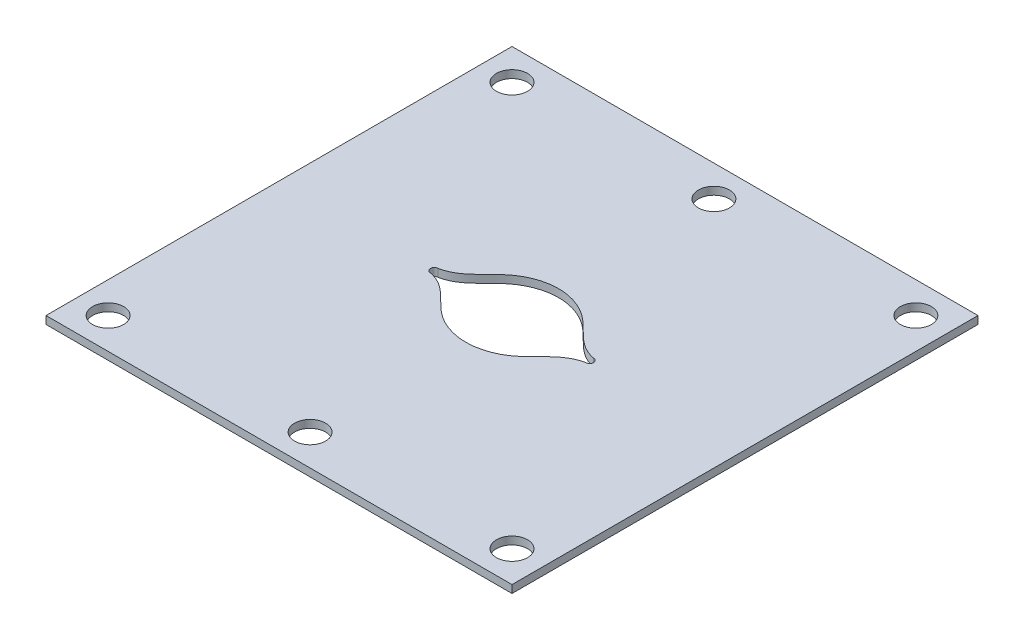
SolidWorks part; units mm, degrees
ref_plane "Front Plane" through (0, 0, 0) normal (0, 0, 1) x (1, 0, 0)
ref_plane "Top Plane" through (0, 0, 0) normal (0, 1, 0) x (1, 0, 0)
ref_plane "Right Plane" through (0, 0, 0) normal (1, 0, 0) x (0, 0, -1)
sketch "Sketch1" plane through (0, 0, 0) normal (0, 1, 0) x (1, 0, 0)
  line L1 (30, -30) -> (-30, -30)
  line L2 (30, -30) -> (30, 30)
  line L3 (30, 30) -> (-30, 30)
  line L4 (-30, -30) -> (-30, 30)
  line L5 (30, -30) -> (-30, 30) construction
  line L6 (30, 30) -> (-30, -30) construction
  point P0 (0, 0)
  dimension "D1" = 60
  dimension "D2" = 60
extrude "Boss-Extrude1" add sketch "Sketch1" along normal blind 1
sketch "Sketch2" plane through (0, 1, 0) normal (0, 1, 0) x (1, 0, 0)
  line L0 (30, 30) -> (-30, 30) construction
  line L2 (-30, 30) -> (-30, -30) construction
  line L3 (30, -30) -> (30, 30) construction
  line L5 (-30, -30) -> (30, -30) construction
  line L7 (-30, 30) -> (-30, -30) construction
  circle A0 centre (-26, 26) radius 2
  circle A1 centre (0, 26) radius 2
  circle A2 centre (26, 26) radius 2
  circle A3 centre (26, -26) radius 2
  circle A4 centre (0, -26) radius 2
  circle A5 centre (-26, -26) radius 2
  dimension "D1" = 4
  dimension "D5" = 4
  dimension "D7" = 4
  dimension "D10" = 4
  dimension "D16" = 4
  dimension "D17" = 4
  dimension "D2" = 4
  dimension "D3" = 4
  dimension "D4" = 4
  dimension "D6" = 0
  dimension "D8" = 4
  dimension "D9" = 4
  dimension "D11" = 4
  dimension "D12" = 4
  dimension "D13" = 4
  dimension "D14" = 4
  dimension "D15" = 4
  dimension "D18" = 0
extrude "Cut-Extrude1" cut sketch "Sketch2" against normal through all
sketch "Sketch3" plane through (0, 1, 0) normal (0, 1, 0) x (1, 0, 0)
  circle A0 centre (10, 0) radius 0.5
  circle A1 centre (-10, 0) radius 0.5
  dimension "D3" = 1
  dimension "D4" = 1
  dimension "D1" = 20
  dimension "D2" = 10
extrude "Cut-Extrude2" cut sketch "Sketch3" against normal through all
sketch "Sketch4" plane through (0, 1, 0) normal (0, 1, 0) x (1, 0, 0)
  circle A0 centre (0, 0) radius 6
  dimension "D1" = 12
sketch "Sketch6" plane through (0, 1, 0) normal (0, 1, 0) x (1, 0, 0)
  line L0 (0, 6) -> (0, -7.4668) construction
  line L1 (10, 0) -> (10, 0.7742) construction
  line L2 (-10, 0) -> (-10, 0.5) construction
  line L3 (-10, 1.8223) -> (-10, -1.2452) construction
  line L4 (10, -1.0662) -> (10, 0) construction
  line L6 (7.5, -1.75) -> (-7.5, -1.75)
  line L7 (7.5, -1.75) -> (7.5, 1.75)
  line L8 (7.5, 1.75) -> (-7.5, 1.75)
  line L9 (-7.5, -1.75) -> (-7.5, 1.75)
  line L10 (7.5, -1.75) -> (-7.5, 1.75) construction
  line L11 (7.5, 1.75) -> (-7.5, -1.75) construction
  line L12 (4.5, -4.5) -> (-4.5, -4.5)
  line L13 (4.5, -4.5) -> (4.5, 4.5)
  line L14 (4.5, 4.5) -> (-4.5, 4.5)
  line L15 (-4.5, -4.5) -> (-4.5, 4.5)
  line L16 (4.5, -4.5) -> (-4.5, 4.5) construction
  line L17 (4.5, 4.5) -> (-4.5, -4.5) construction
  circle A0 centre (0, 0) radius 6 construction
  circle A1 centre (-10, 0) radius 0.5 construction
  point P16 (0, 0)
  point P21 (0, 0)
  dimension "D3" = 9
  dimension "D1" = 15
  dimension "D2" = 3.5
  dimension "D4" = 9
sketch "Sketch7" plane through (0, 1, 0) normal (0, 1, 0) x (1, 0, 0)
  line L0 (10, 0) -> (10, 0.7742) construction
  line L1 (-10, 1.8223) -> (-10, -1.2452) construction
  line L3 (10, -1.0662) -> (10, 0) construction
  circle A0 centre (10, 0) radius 0.5 construction
  circle A1 centre (-10, 0) radius 0.5 construction
  spline S0 degree 3 poles (10, 0.5) (7.5419, 0.9716) (5.542, 4.6336) (0, 6.5583) (-5.542, 4.6336) (-7.5419, 0.9716) (-10, 0.5) knots 0 0 0 0 0.295687 0.5 0.704313 1 1 1 1
  spline S1 degree 3 poles (10, -0.5) (7.5396, -0.9609) (5.5515, -4.6629) (0, -6.4827) (-5.5515, -4.6629) (-7.5396, -0.9609) (-10, -0.5) knots 0 0 0 0 0.296041 0.5 0.703959 1 1 1 1
  spline S2 degree 2 poles (-10, 0.5) (-11, 0) (-10, -0.5) knots 0 0 0 1 1 1
  spline S3 degree 2 poles (10, 0.5) (11, 0) (10, -0.5) knots 0 0 0 1 1 1
extrude "Cut-Extrude3" cut sketch "Sketch7" against normal blind 10
